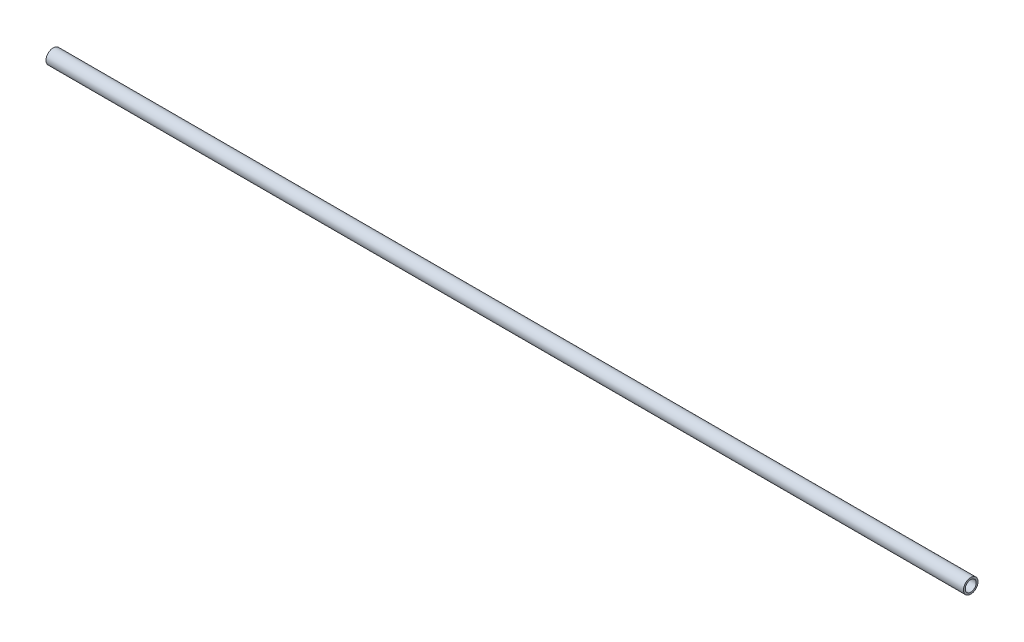
SolidWorks part; units mm, degrees
ref_plane "Front" through (0, 0, 0) normal (0, 0, 1) x (1, 0, 0)
ref_plane "Top" through (0, 0, 0) normal (0, 1, 0) x (1, 0, 0)
ref_plane "Right" through (0, 0, 0) normal (1, 0, 0) x (0, 0, -1)
sketch "Sketch2" plane through (0, 0, 0) normal (1, 0, 0) x (0, 0, -1)
  circle A0 centre (0, 0) radius 8
  circle A1 centre (0, 0) radius 6
  dimension "D1" = 16
  dimension "D2" = 12
extrude "Boss-Extrude1" add sketch "Sketch2" along normal blind 1016
ref_plane "Plane1" through (0, 8, 0) normal (0, 1, 0) x (1, 0, 0)
sketch "Sketch3" plane through (0, 8, 0) normal (0, 1, 0) x (1, 0, 0)
  line L0 (0, 8) -> (0, -8) construction
  line L1 (0, 45.531) -> (6.35, 45.531)
  line L2 (0, 45.531) -> (0, -49.6761)
  line L3 (0, -49.6761) -> (6.35, -49.6761)
  line L4 (6.35, 45.531) -> (6.35, -49.6761)
  dimension "D1" = 6.35
extrude "Cut-Extrude1" cut sketch "Sketch3" against normal through all
